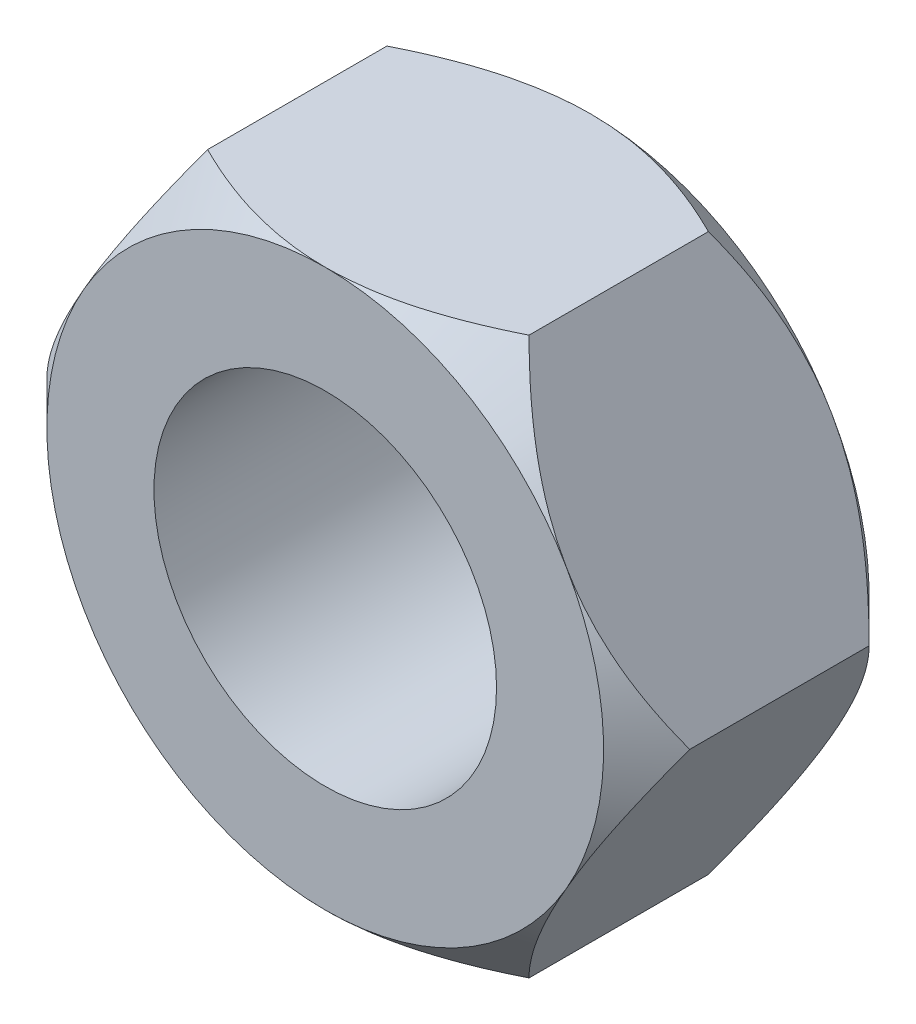
SolidWorks part; units mm, degrees
ref_plane "Plano frontal" through (0, 0, 0) normal (0, 0, 1) x (1, 0, 0)
ref_plane "Plano superior" through (0, 0, 0) normal (0, 1, 0) x (1, 0, 0)
ref_plane "Plano direito" through (0, 0, 0) normal (1, 0, 0) x (0, 0, -1)
sketch "Esboço1" plane through (0, 0, 0) normal (0, 0, 1) x (1, 0, 0)
  line L1 (3.7528, -6.5) -> (7.5056, 0)
  line L2 (7.5056, 0) -> (3.7528, 6.5)
  line L3 (3.7528, 6.5) -> (-3.7528, 6.5)
  line L4 (-3.7528, 6.5) -> (-7.5056, 0)
  line L5 (-7.5056, 0) -> (-3.7528, -6.5)
  line L6 (-3.7528, -6.5) -> (3.7528, -6.5)
  circle A0 centre (0, 0) radius 6.5 construction
  circle A1 centre (0, 0) radius 4
extrude "Ressalto-extrusão1" add sketch "Esboço1" along normal blind 6.2
sketch "Esboço2" plane through (0, 0, 6.2) normal (0, 0, 1) x (1, 0, 0)
  circle A0 centre (0, 0) radius 6.5
extrude "Corte-extrusão1" cut sketch "Esboço2" against normal blind 6.2 draft 45 flip side to cut
sketch "Esboço3" plane through (0, 0, 0) normal (0, 0, -1) x (-1, 0, 0)
  circle A0 centre (0, 0) radius 6.5
extrude "Corte-extrusão2" cut sketch "Esboço3" against normal blind 6.2 draft 45 flip side to cut
